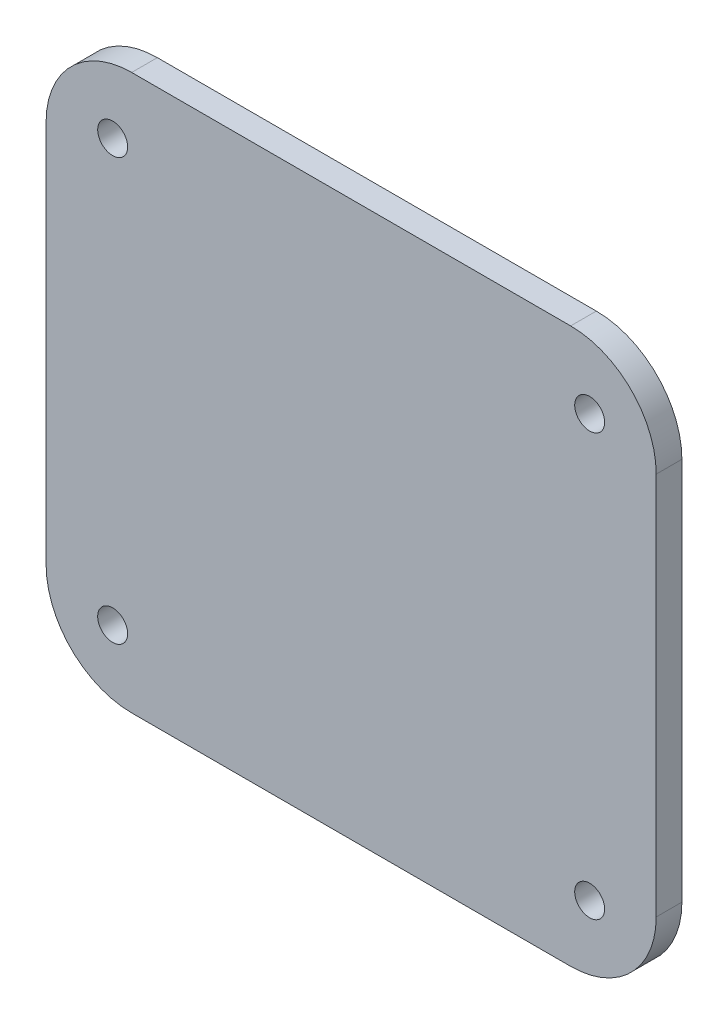
SolidWorks part; units mm, degrees
ref_plane "前视基准面" through (0, 0, 0) normal (0, 0, 1) x (1, 0, 0)
ref_plane "上视基准面" through (0, 0, 0) normal (0, 1, 0) x (1, 0, 0)
ref_plane "右视基准面" through (0, 0, 0) normal (1, 0, 0) x (0, 0, -1)
sketch "草图1" plane through (0, 0, 0) normal (0, 0, 1) x (1, 0, 0)
  line L0 (28.2003, 24.6475) -> (-27.5405, 24.6475) construction
  line L1 (-27.5405, 24.6475) -> (-27.5405, -24.6117) construction
  line L2 (-27.5405, -24.6117) -> (28.2003, -24.6117) construction
  line L3 (28.2003, -24.6117) -> (28.2003, 24.6475) construction
  line L4 (-22.3553, -19.4266) -> (23.0151, -19.4266)
  line L5 (23.0151, -19.4266) -> (23.0151, 19.4623)
  line L6 (23.0151, 19.4623) -> (-22.3553, 19.4623)
  line L7 (-22.3553, 19.4623) -> (-22.3553, -19.4266)
  line L8 (-35.3182, -32.3895) -> (35.9781, -32.3895)
  line L9 (35.9781, -32.3895) -> (35.9781, 32.4253)
  line L10 (35.9781, 32.4253) -> (-35.3182, 32.4253)
  line L11 (-35.3182, 32.4253) -> (-35.3182, -32.3895)
  circle A0 centre (-27.5405, 24.6475) radius 1.75
  circle A1 centre (28.2003, 24.6475) radius 1.75
  circle A2 centre (28.2003, -24.6117) radius 1.75
  circle A3 centre (-27.5405, -24.6117) radius 1.75
  dimension "D1" = 3.5
  dimension "D2" = 3.5
extrude "凸台-拉伸1" add sketch "草图1" along normal blind 3 contours L10 L11 L8 L9 A3 A2 A1 A0 L7 L6 L5 L4 | L6 L7 L4 L5
fillet "圆角1" radius 10 4 edges at (-35.3182, -32.3895, 1.5) (35.9781, -32.3895, 1.5) (35.9781, 32.4253, 1.5) (-35.3182, 32.4253, 1.5)
